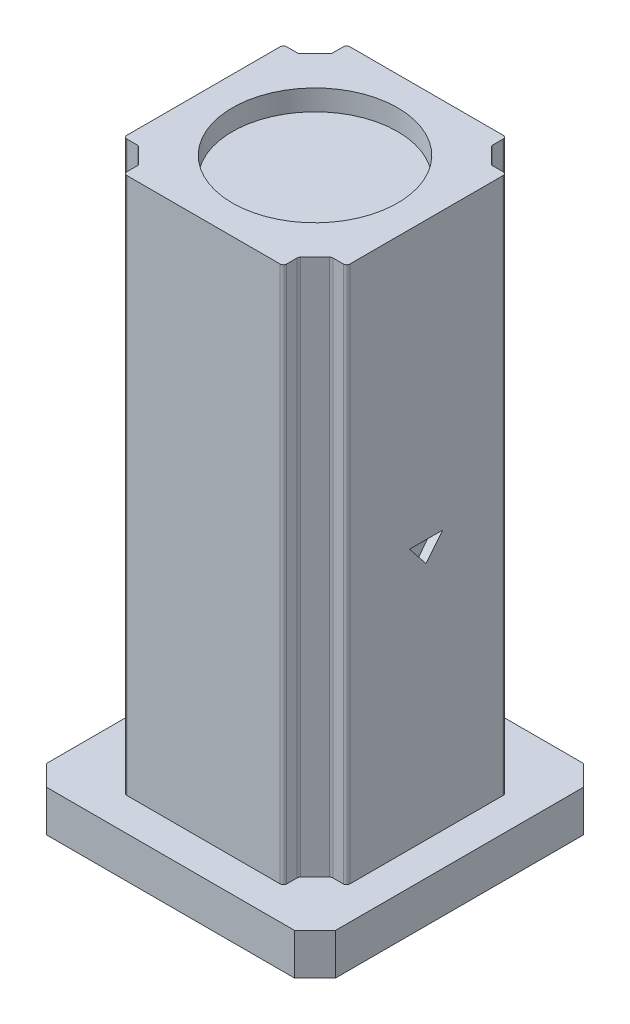
SolidWorks part; units mm, degrees
ref_plane "Front Plane" through (0, 0, 0) normal (0, 0, 1) x (1, 0, 0)
ref_plane "Top Plane" through (0, 0, 0) normal (0, 1, 0) x (1, 0, 0)
ref_plane "Right Plane" through (0, 0, 0) normal (1, 0, 0) x (0, 0, -1)
sketch "Sketch1" plane through (0, 0, 0) normal (0, 1, 0) x (1, 0, 0)
  line L0 (-35, 30) -> (-30, 35)
  line L1 (-30, -35) -> (30, -35)
  line L2 (-35, -30) -> (-35, 30)
  line L3 (-30, 35) -> (30, 35)
  line L4 (35, -30) -> (35, 30)
  line L5 (-35, -35) -> (35, 35) construction
  line L6 (-35, 35) -> (35, -35) construction
  line L7 (30, 35) -> (35, 30)
  line L8 (30, -35) -> (35, -30)
  line L9 (-35, -30) -> (-30, -35)
  point P0 (0, 0)
  dimension "D1" = 70
  dimension "D2" = 70
  dimension "D3" = 5
  dimension "D4" = 45
  dimension "D5" = 5
  dimension "D6" = 45
  dimension "D7" = 5
  dimension "D8" = 45
  dimension "D9" = 5
  dimension "D10" = 45
extrude "Boss-Extrude1" add sketch "Sketch1" along normal blind 10 contours L0 L3 L7 L4 L8 L1 L9 L2
sketch "Sketch2" plane through (0, 10, 0) normal (0, 1, 0) x (1, 0, 0)
  line L8 (-23.3431, 19.3431) -> (-19.3431, 23.3431)
  line L9 (0, -21.3431) -> (0, 21.3431) construction
  line L10 (-41.7571, 0) -> (41.7571, 0) construction
  line L11 (-27, 19.3431) -> (-23.3431, 19.3431)
  line L12 (-19.3431, 27) -> (-19.3431, 23.3431)
  line L13 (27, 19.3431) -> (23.3431, 19.3431)
  line L15 (-21.3431, 21.3431) -> (-19.3431, 19.3431) construction
  line L16 (-27, 26.6863) -> (-27, -26.6863)
  line L17 (-26.6863, -27) -> (26.6863, -27)
  line L18 (27, -26.6863) -> (27, 26.6863)
  line L19 (26.6863, 27) -> (-26.6863, 27)
  line L20 (-27, 19.3431) -> (-27, -19.3431)
  line L21 (-19.3431, -27) -> (19.3431, -27)
  line L22 (27, -19.3431) -> (27, 19.3431)
  line L23 (19.3431, 27) -> (-19.3431, 27)
  line L24 (-27, -26.6863) -> (-26.6863, -27)
  line L26 (26.6863, -27) -> (27, -26.6863)
  line L28 (27, 26.6863) -> (26.6863, 27)
  line L30 (-26.6863, 27) -> (-27, 26.6863)
  line L32 (23.3431, 19.3431) -> (19.3431, 23.3431)
  line L33 (19.3431, 27) -> (19.3431, 23.3431)
  line L34 (27, -19.3431) -> (23.3431, -19.3431)
  line L35 (23.3431, -19.3431) -> (19.3431, -23.3431)
  line L36 (19.3431, -27) -> (19.3431, -23.3431)
  line L37 (-19.3431, -27) -> (-19.3431, -23.3431)
  line L38 (-23.3431, -19.3431) -> (-19.3431, -23.3431)
  line L39 (-27, -19.3431) -> (-23.3431, -19.3431)
  point P0 (-26.8431, 26.8431)
  point P8 (0, 0)
  point P13 (0, 0)
  dimension "D4" = 4
  dimension "D5" = 45
  dimension "D1" = 8
extrude "Boss-Extrude2" add sketch "Sketch2" along normal blind 130
fillet "Fillet1" radius 0.8 16 edges at (27, 75, -19.3431) (23.3431, 75, -19.3431) (19.3431, 75, -23.3431) (19.3431, 75, -27) (-19.3431, 75, -27) (-19.3431, 75, -23.3431) (-23.3431, 75, -19.3431) (-27, 75, 19.3431) (-23.3431, 75, 19.3431) (-19.3431, 75, 23.3431) (-19.3431, 75, 27) (19.3431, 75, 27) (19.3431, 75, 23.3431) (23.3431, 75, 19.3431) (27, 75, 19.3431) (-27, 75, -19.3431)
sketch "Sketch3" plane through (0, 140, 0) normal (0, 1, 0) x (1, 0, 0)
  circle A0 centre (0, 0) radius 20
  dimension "D1" = 40
extrude "Cut-Extrude1" cut sketch "Sketch3" against normal blind 5
sketch "Sketch5" plane through (27, 0, 0) normal (1, 0, 0) x (0, 0, -1)
  line L0 (-4.1123, 72.968) -> (3.8877, 72.968)
  line L1 (-4.1123, 72.968) -> (-0.1123, 67.968)
  line L2 (-0.1123, 67.968) -> (3.8877, 72.968)
  point P3 (-0.1123, 72.968)
  dimension "D1" = 8
  dimension "D2" = 5
extrude "Cut-Extrude2" cut sketch "Sketch5" against normal blind 2
